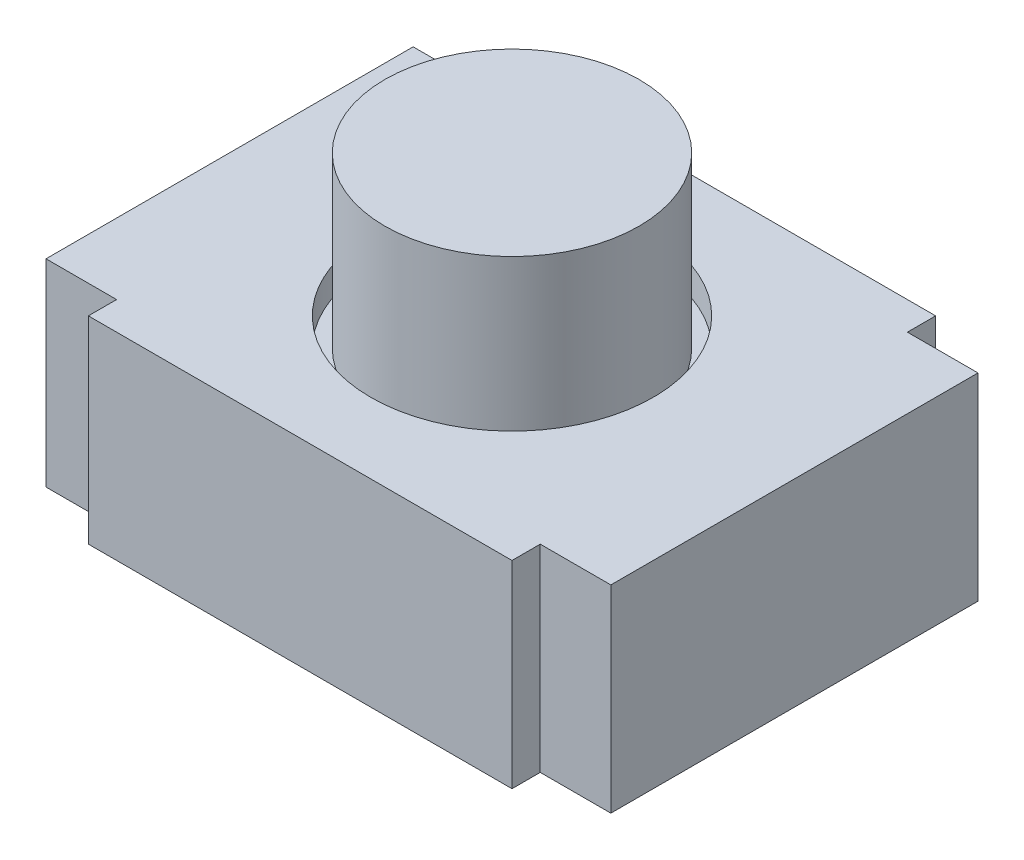
SolidWorks part; units mm, degrees
ref_plane "Front Plane" through (0, 0, 0) normal (0, 0, 1) x (1, 0, 0)
ref_plane "Top Plane" through (0, 0, 0) normal (0, 1, 0) x (1, 0, 0)
ref_plane "Right Plane" through (0, 0, 0) normal (1, 0, 0) x (0, 0, -1)
sketch "Sketch1" plane through (0, 0, 0) normal (0, 1, 0) x (1, 0, 0)
  line L1 (-2, 1.3) -> (2, 1.3)
  line L2 (-2, 1.3) -> (-2, -1.3)
  line L3 (-2, -1.3) -> (2, -1.3)
  line L4 (2, 1.3) -> (2, -1.3)
  line L5 (-2, 1.3) -> (2, -1.3) construction
  line L6 (-2, -1.3) -> (2, 1.3) construction
  point P0 (0, 0)
  dimension "Length" = 4
  dimension "Width" = 2.6
extrude "Boss-Extrude1" add sketch "Sketch1" against normal blind 1.2
sketch "Sketch2" plane through (0, 0, 0) normal (0, 1, 0) x (1, 0, 0)
  line L1 (-1.5, 1.5) -> (1.5, 1.5)
  line L2 (-1.5, 1.5) -> (-1.5, 1.3)
  line L3 (-1.5, -1.5) -> (1.5, -1.5)
  line L4 (1.5, 1.5) -> (1.5, 1.3)
  line L5 (-1.5, 1.5) -> (1.5, -1.5) construction
  line L6 (-1.5, -1.5) -> (1.5, 1.5) construction
  line L7 (-1.5, 1.3) -> (-2, 1.3)
  line L8 (-2, 1.3) -> (-2, -1.3)
  line L9 (-2, 1.3) -> (-2, -1.3) construction
  line L10 (-2, -1.3) -> (-1.5, -1.3)
  line L11 (1.5, 1.3) -> (2, 1.3)
  line L12 (2, -1.3) -> (2, 1.3) construction
  line L13 (2, 1.3) -> (2, -1.3)
  line L14 (2, -1.3) -> (1.5, -1.3)
  line L15 (-1.5, -1.3) -> (-1.5, -1.5)
  line L16 (1.5, -1.3) -> (1.5, -1.5)
  point P0 (0, 0)
  dimension "D1" = 3
  dimension "D2" = 3
extrude "Boss-Extrude2" add sketch "Sketch2" along normal blind 0.2 separate body
sketch "Sketch3" plane through (0, 0, 0) normal (0, -1, 0) x (-1, 0, 0)
  line L1 (1.5, -1.5) -> (-1.5, -1.5)
  line L2 (1.5, -1.5) -> (1.5, -1.3)
  line L3 (1.5, -1.3) -> (-1.5, -1.3)
  line L4 (-1.5, -1.5) -> (-1.5, -1.3)
  line L5 (-1.5, 1.5) -> (1.5, 1.5)
  line L6 (-1.5, 1.5) -> (-1.5, 1.3)
  line L7 (-1.5, 1.3) -> (1.5, 1.3)
  line L8 (1.5, 1.5) -> (1.5, 1.3)
extrude "Boss-Extrude3" add sketch "Sketch3" along normal up to surface (1.2 mm away) up to face at (0, -1.2, 0)
sketch "Sketch4" plane through (0, 0.2, 0) normal (0, 1, 0) x (1, 0, 0)
  circle A0 centre (0, 0) radius 1
  dimension "Dia" = 2
extrude "Cut-Extrude1" cut sketch "Sketch4" against normal up to next (0.2 mm away)
sketch "Sketch5" plane through (0, 0, 0) normal (0, 1, 0) x (1, 0, 0)
  circle A0 centre (0, 0) radius 0.9
  dimension "Dia" = 1.8
extrude "Boss-Extrude4" add sketch "Sketch5" along normal offset from surface (1.2 mm away) 1 up to face at (0, 0.2, 1) offset beyond the face yes
sketch "Sketch6" plane through (0, -1.2, 0) normal (0, -1, 0) x (1, 0, 0)
  point P0 (0, 0)
